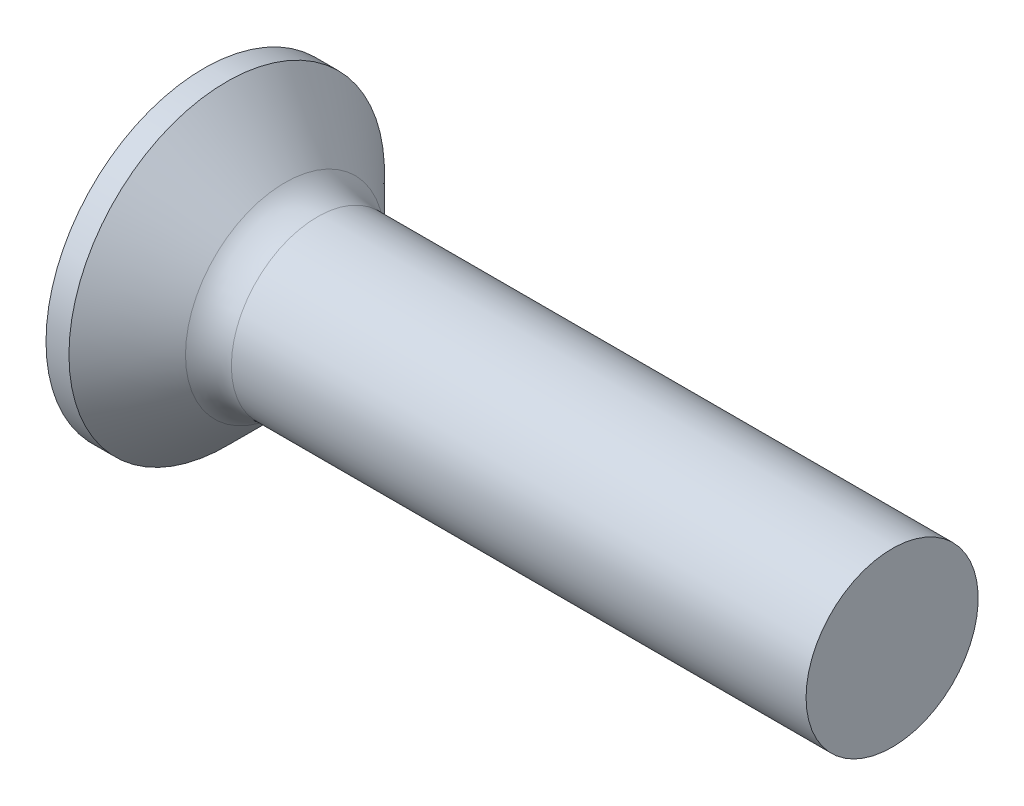
SolidWorks part; units mm, degrees
revolve "Base-Revolve" add sketch "BodySke"
sketch "BodySke" plane through (0, 0, 0) normal (0, 0, 1) x (1, 0, 0)
  line L0 (0, 0) -> (0, 2.75)
  line L1 (0, 2.75) -> (0.4, 2.75)
  line L2 (1.65, 1.5) -> (12, 1.5)
  line L3 (12, 1.5) -> (12, 0)
  line L4 (12, 0) -> (0, 0)
  line L5 (-6.35, 0) -> (82.55, 0) construction
  line L6 (1.65, -1.5) -> (12, -1.5) construction
  line L7 (0.4, -2.75) -> (1.65, -1.5) construction
  line L8 (0.4, 2.75) -> (1.65, 1.5)
  line L9 (0, -2.75) -> (0.4, -2.75) construction
  line L10 (2.15, 3.0875) -> (2.15, -6.4375) construction
  line L11 (-4, 6.35) -> (-4, -3.175) construction
  dimension "Diameter" = 3
  dimension "Length" = 12
  dimension "Head_ht" = 1.65
  dimension "Head_dia" = 5.5
  dimension "Head_ang" = 90
  dimension "D6" = 0.4
  dimension "Advance" = 0.5
cosmetic thread "ThreadCosmetic" [suppressed]
fillet "Fillet1" radius 0.8 1 edges at (1.65, 0, 1.5)
ref_plane "Plane1" through (0, 0, 0) normal (0, 0, 1) x (1, 0, 0)
ref_plane "Plane2" through (0, 0, 0) normal (0, 1, 0) x (1, 0, 0)
ref_plane "Plane3" through (0, 0, 0) normal (1, 0, 0) x (0, 0, -1)
sketch "Sketch3" plane through (0, 0, 0) normal (-1, 0, 0) x (0, 0, 1)
  line L0 (-0.37, 1.5) -> (0.37, 1.5)
  line L1 (0.37, 1.5) -> (0.37, -1.5)
  line L2 (0.37, -1.5) -> (-0.37, -1.5)
  line L3 (-0.37, -1.5) -> (-0.37, 1.5)
  dimension "Cross_dia" = 3
  dimension "Cross_width" = 0.74
  dimension "D1" = 1.5
  dimension "D2" = 0.37
ref_plane "Plane4" through (2.01, 0, 0) normal (-1, 0, 0) x (0, 0, 1)
sketch "Sketch4" plane through (2.01, 0, 0) normal (-1, 0, 0) x (0, 0, 1)
  line L0 (-0.37, 0.4979) -> (0.37, 0.4979)
  line L3 (0.37, 0.4979) -> (0.37, -0.4979)
  line L4 (0.37, -0.4979) -> (-0.37, -0.4979)
  line L5 (-0.37, -0.4979) -> (-0.37, 0.4979)
  dimension "D2" = 0.9957
  dimension "D1" = 0.74
  dimension "D4" = 0.4979
  dimension "D3" = 0.37
loft "Recess" cut profiles "Sketch3", "Sketch4"
pattern_circular "RecPat" count 2 every 90 about axis through (0, 0, 0) along (1, 0, 0) of "Recess"
sketch "RecCorSke" plane through (0, 0, 0) normal (0, 0, 1) x (1, 0, 0)
  line L0 (-3.175, 0) -> (15.875, 0) construction
  line L2 (0, 0) -> (0, 0.6966)
  line L3 (0, 0.6966) -> (2.01, 0.556)
  line L4 (2.01, 0.556) -> (2.1907, 0)
  line L5 (2.1907, 0) -> (0, 0)
  dimension "Diameter" = 1.112
  dimension "Depth" = 2.01
  dimension "Draft_angle" = 4
  dimension "Bottom_angle" = 18
revolve "RecessCore" cut sketch "RecCorSke" angle 360 about L0
sketch "ThdSchSke" plane through (0, 0, 0) normal (0, 0, 1) x (1, 0, 0)
  line L0 (2.15, -1.2195) -> (1.9536, -1.5)
  line L1 (2.15, -1.2195) -> (2.3464, -1.5)
  line L2 (2.3464, -1.5) -> (2.3464, -1.875)
  line L3 (-3.175, 0) -> (5.1513, 0) construction
  line L5 (2.3464, -1.875) -> (1.9536, -1.875)
  line L6 (1.9536, -1.875) -> (1.9536, -1.5)
  line L7 (0, 2.75) -> (0, -2.75) construction
  dimension "Diameter" = 3
  dimension "Thread_minor" = 2.439
  dimension "Start" = 2.15
revolve "ThreadSchematic" [suppressed] cut sketch "ThdSchSke" angle 360 about L3
pattern_linear "ThdSchPat" [suppressed]
equation "\"D1@Sketch3\" = \"Cross_dia@Sketch3\" / 2"
equation "\"D2@Sketch3\" = \"Cross_width@Sketch3\" / 2"
equation "\"Depth@RecCorSke\" = \"Cross_depth@Plane4\""
equation "\"D1@Sketch4\" = \"Cross_width@Sketch3\""
equation "\"D2@Sketch4\" = \"Cross_dia@Sketch3\" - 2.0 * \"Cross_depth@Plane4\" * tan(26.5  * 0.017453292)"
equation "\"D3@Sketch4\" = \"D1@Sketch4\" / 2"
equation "\"D4@Sketch4\" = \"D2@Sketch4\" / 2"
equation "\"Thread_length@ThreadCosmetic\" = ((sgn( (\"Length@BodySke\" - \"Advance@BodySke\" * 1.0 - \"Head_ht@BodySke\" ) - \"Thread_nom@BodySke\" )-1)*( (\"Length@BodySke\" - \"Advance@BodySke\" * 1.0 - \"Head_ht@BodySke\" ) - \"Thread_nom@BodySke\" ))/-2+ \"Thread_nom@BodySke\""
equation "\"Thread_minor@ThdSchSke\" = \"Thread_minor@ThreadCosmetic\""
equation "\"Diameter@ThdSchSke\" = \"Diameter@BodySke\""
equation "\"Overcut@ThdSchSke\" = \"Diameter@BodySke\" * 1.25"
equation "\"Start@ThdSchSke\" = 0.000001 + \"Length@BodySke\" - \"Thread_length@ThreadCosmetic\"  '---Countersunk---"
equation "\"Num_threads@ThdSchPat\" = int( \"Thread_length@ThreadCosmetic\" / \"Advance@BodySke\" + 0.999 )  + 1"
equation "\"Advance@ThdSchPat\" = \"Thread_length@ThreadCosmetic\" /  (\"Num_threads@ThdSchPat\" - 1) 'relax it"
